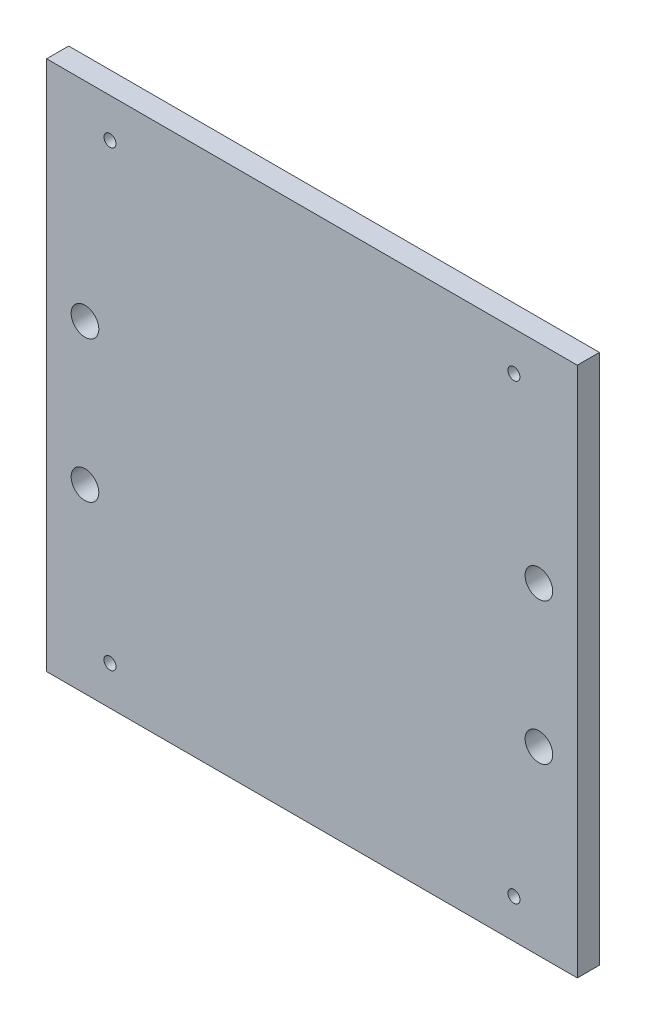
SolidWorks part; units mm, degrees
material "6061-T6 (SS)"
ref_plane "Front Plane" through (0, 0, 0) normal (0, 0, 1) x (1, 0, 0)
ref_plane "Top Plane" through (0, 0, 0) normal (0, 1, 0) x (1, 0, 0)
ref_plane "Right Plane" through (0, 0, 0) normal (1, 0, 0) x (0, 0, -1)
sketch "Sketch1" plane through (0, 0, 0) normal (0, 0, 1) x (1, 0, 0)
  line L0 (0, 187.525) -> (0, 38.475) construction
  line L1 (-67.525, 187.525) -> (67.525, 187.525) construction
  line L2 (-67.525, 187.525) -> (-67.525, 38.475) construction
  line L3 (-67.525, 38.475) -> (67.525, 38.475) construction
  line L4 (67.525, 187.525) -> (67.525, 38.475) construction
  line L6 (-76.2, 36.8) -> (76.2, 36.8)
  line L7 (-76.2, 36.8) -> (-76.2, 189.2)
  line L8 (-76.2, 189.2) -> (76.2, 189.2)
  line L9 (76.2, 36.8) -> (76.2, 189.2)
  line L10 (-76.2, 36.8) -> (76.2, 189.2) construction
  line L11 (-76.2, 189.2) -> (76.2, 36.8) construction
  circle A0 centre (-58, 178) radius 3 construction
  circle A1 centre (58, 48) radius 3 construction
  point P10 (0, 113)
  point P15 (0, 187.525)
  dimension "D2" = 9.525
  dimension "D3" = 9.525
  dimension "D4" = 9.525
  dimension "D1" = 9.525
  dimension "D5" = 152.4
  dimension "D6" = 152.4
extrude "Boss-Extrude1" add sketch "Sketch1" along normal blind 6.35
hole_wizard "5/16 (0.3125) Diameter Hole1" positions "Sketch2" profile "Sketch3" hole size "5/16" standard "ANSI Inch" end condition up to next
sketch "Sketch2" plane through (0, 0, 0) normal (0, 0, -1) x (-1, 0, 0)
  line L1 (0, 189.2) -> (0, 36.8) construction
  line L3 (76.2, 36.8) -> (-76.2, 36.8) construction
  line L5 (-76.2, 189.2) -> (76.2, 189.2) construction
  circle A0 centre (65.1764, 88.807) radius 2.5527 construction
  circle A1 centre (65.1764, 129.447) radius 2.5527 construction
  point P0 (65.1764, 88.807)
  point P2 (65.1764, 129.447)
  point P24 (0, 36.8)
  point P27 (18.2952, 178.8394)
  point P30 (0, 189.2)
  point P31 (-65.1764, 129.447)
  point P32 (-65.1764, 88.807)
sketch "Sketch3" plane through (-65.1764, 88.807, 0) normal (1, 0, 0) x (0, 1, 0)
  line L0 (0, 0) -> (0, 6.35)
  line L1 (0, 6.35) -> (3.9687, 6.35)
  line L2 (3.9687, 6.35) -> (3.9687, 0)
  line L5 (3.9687, 0) -> (0, 0)
  line L11 (0, -6.35) -> (0, 107.95) construction
  dimension "Thru Hole Dia." = 7.9375
  dimension "Thru Hole Depth" = 6.35
hole_wizard "#8-32 Tapped Hole1" positions "Sketch4" profile "Sketch5" tap size "#8-32" standard "ANSI Inch" end condition up to next
sketch "Sketch4" plane through (0, 0, 0) normal (0, 0, -1) x (-1, 0, 0)
  point P0 (-58, 178)
  point P3 (58, 178)
  point P6 (58, 48)
  point P9 (-58, 48)
sketch "Sketch5" plane through (58, 178, 0) normal (1, 0, 0) x (0, 1, 0)
  line L0 (0, 0) -> (0, 6.35)
  line L1 (0, 6.35) -> (1.7272, 6.35)
  line L2 (1.7272, 6.35) -> (1.7272, 0)
  line L5 (1.7272, 0) -> (0, 0)
  line L11 (0, -6.35) -> (0, 107.95) construction
  dimension "Thru Tap Drill Dia." = 3.4544
  dimension "Thru Tap Drill Depth" = 6.35
cosmetic thread "Hole Thread1"
cosmetic thread "Hole Thread2"
cosmetic thread "Hole Thread3"
cosmetic thread "Hole Thread4"
